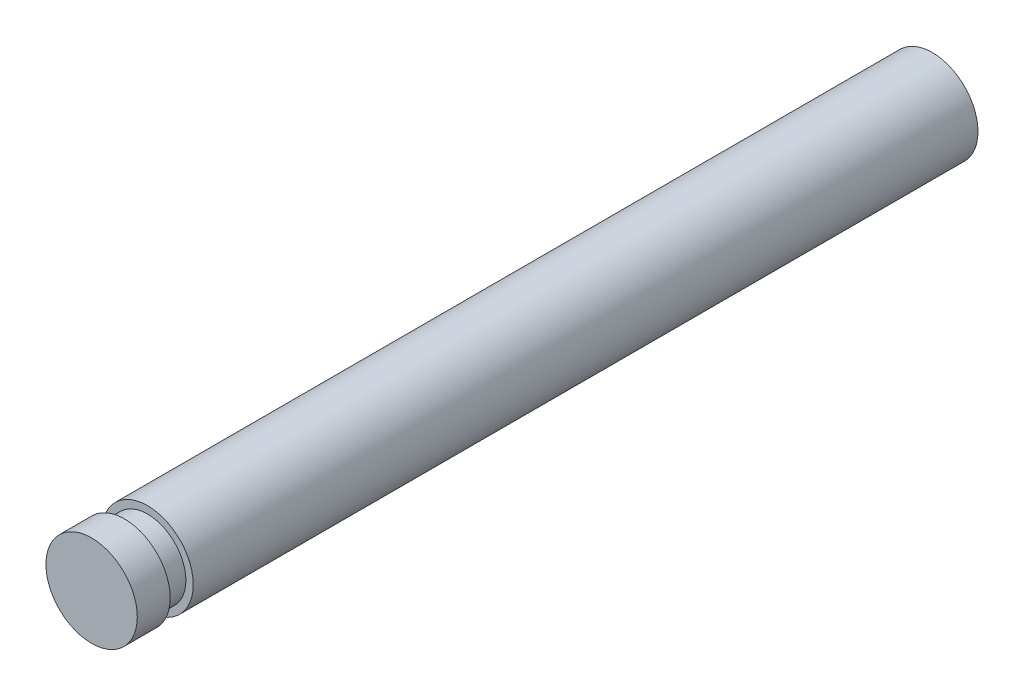
SolidWorks part; units mm, degrees
ref_plane "Front Plane" through (0, 0, 0) normal (0, 0, 1) x (1, 0, 0)
ref_plane "Top Plane" through (0, 0, 0) normal (0, 1, 0) x (1, 0, 0)
ref_plane "Right Plane" through (0, 0, 0) normal (1, 0, 0) x (0, 0, -1)
sketch "Sketch1" plane through (0, 0, 0) normal (0, 0, 1) x (1, 0, 0)
  circle A0 centre (0, 0) radius 3.175
  dimension "D1" = 6.35
extrude "Boss-Extrude1" add sketch "Sketch1" against normal blind 54.5338
sketch "Sketch2" plane through (0, 0, 0) normal (0, 0, 1) x (1, 0, 0)
  circle A0 centre (0, 0) radius 2.667
  dimension "D1" = 5.334
extrude "Boss-Extrude2" add sketch "Sketch2" along normal blind 1.6002
sketch "Sketch3" plane through (0, 0, 1.6002) normal (0, 0, 1) x (1, 0, 0)
  circle A0 centre (0, 0) radius 3.175
  dimension "D1" = 6.35
extrude "Boss-Extrude3" add sketch "Sketch3" along normal blind 2.286
